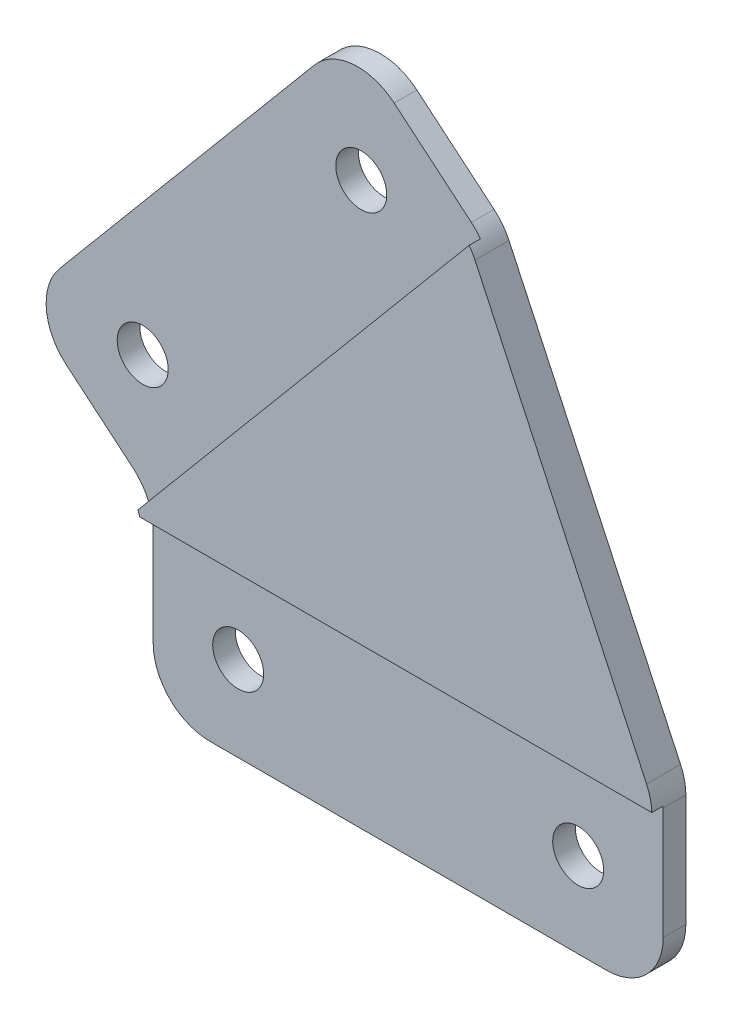
SolidWorks part; units mm, degrees
material "3.1325 (EN-AW 2017A)"
ref_plane "正面" through (0, 0, 0) normal (0, 0, 1) x (1, 0, 0)
ref_plane "平面" through (0, 0, 0) normal (0, 1, 0) x (1, 0, 0)
ref_plane "右側面" through (0, 0, 0) normal (1, 0, 0) x (0, 0, -1)
sketch "ｽｹｯﾁ1" plane through (0, 0, 0) normal (0, 0, 1) x (1, 0, 0)
  line L0 (0, 0) -> (306.8848, 365.731) construction
  line L1 (306.8848, 365.731) -> (440, 0) construction
  line L2 (440, 0) -> (0, 0) construction
  line L3 (306.8848, 365.731) -> (306.8848, 0) construction
  line L4 (306.8848, 365.731) -> (0, 0) construction
  line L9 (306.8848, 365.731) -> (295.3941, 375.3729)
  line L13 (0, 0) -> (0, -16)
  line L14 (0, -16) -> (45, -16)
  line L15 (45, -16) -> (45, 0)
  line L16 (45, 0) -> (28.9254, 34.472)
  line L17 (28.9254, 34.472) -> (17.4348, 44.1138)
  line L18 (17.4348, 44.1138) -> (-11.4907, 9.6418)
  line L19 (-11.4907, 9.6418) -> (0, 0)
  dimension "D4" = 16
  dimension "D5" = 15
  dimension "D6" = 45
  dimension "D1" = 440
  dimension "D2" = 70
  dimension "D3" = 50
  dimension "D7" = 45
extrude "ﾎﾞｽ - 押し出し1" add sketch "ｽｹｯﾁ1" along normal blind 3 contours L18 L19 L13 L14 L15 L16 L17
sketch "ｽｹｯﾁ2" plane through (0, 0, 3) normal (0, 0, 1) x (1, 0, 0)
  line L0 (0, 0) -> (0, -16) construction
  line L1 (45, -16) -> (45, 0) construction
  line L2 (0, -16) -> (45, -16) construction
  line L3 (-11.4907, 9.6418) -> (0, 0) construction
  line L4 (17.4348, 44.1138) -> (-11.4907, 9.6418) construction
  line L5 (28.9254, 34.472) -> (17.4348, 44.1138) construction
  circle A0 centre (7.5, -8.5) radius 2.25
  circle A1 centre (-0.9244, 10.5662) radius 2.25
  circle A2 centre (18.3592, 33.5476) radius 2.25
  circle A3 centre (37.5, -8.5) radius 2.25
  dimension "D1" = 7.5
  dimension "D2" = 7.5
  dimension "D3" = 7.5
  dimension "D4" = 7.5
  dimension "D5" = 4.5
  dimension "D6" = 4.5
  dimension "D7" = 4.5
  dimension "D8" = 4.5
  dimension "D9" = 7.5
  dimension "D10" = 7.5
  dimension "D11" = 7.5
  dimension "D12" = 7.5
extrude "ｶｯﾄ - 押し出し1" cut sketch "ｽｹｯﾁ2" against normal blind 3
fillet "ﾌｨﾚｯﾄ1" radius 5 7 edges at (28.9254, 34.472, 1.5) (45, 0, 1.5) (45, -16, 1.5) (0, -16, 1.5) (0, 0, 1.5) (-11.4907, 9.6418, 1.5) (17.4348, 44.1138, 1.5)
sketch "ｽｹｯﾁ3" plane through (0, 0, 3) normal (0, 0, 1) x (1, 0, 0)
  line L0 (17.4348, 44.1138) -> (-12.1335, 8.8758)
  line L1 (17.4348, 44.1138) -> (28.9637, 34.4399)
  line L2 (-12.1335, 8.8758) -> (-0.6045, -0.7982)
  line L3 (28.9637, 34.4399) -> (-0.6045, -0.7982)
  line L4 (14.2208, 40.2836) -> (-8.2767, 13.472) construction
  line L5 (-1, -16) -> (45, -16)
  line L6 (-1, -16) -> (-1, -0.95)
  line L7 (45, -16) -> (45, -0.95)
  line L8 (-1, -0.95) -> (45, -0.95)
  line L9 (5, -16) -> (40, -16) construction
  line L10 (28.0763, 35.1845) -> (21.265, 40.8999) construction
  line L11 (45, -11) -> (45, -1.1085) construction
  line L12 (0, -2.3315) -> (0, -11) construction
  line L13 (-7.6604, 6.4279) -> (-1.7861, 1.4987) construction
  dimension "D1" = 15.05
  dimension "D2" = 15.05
  dimension "D3" = 1
  dimension "D4" = 1
extrude "ｶｯﾄ - 押し出し2" cut sketch "ｽｹｯﾁ3" against normal blind 1
